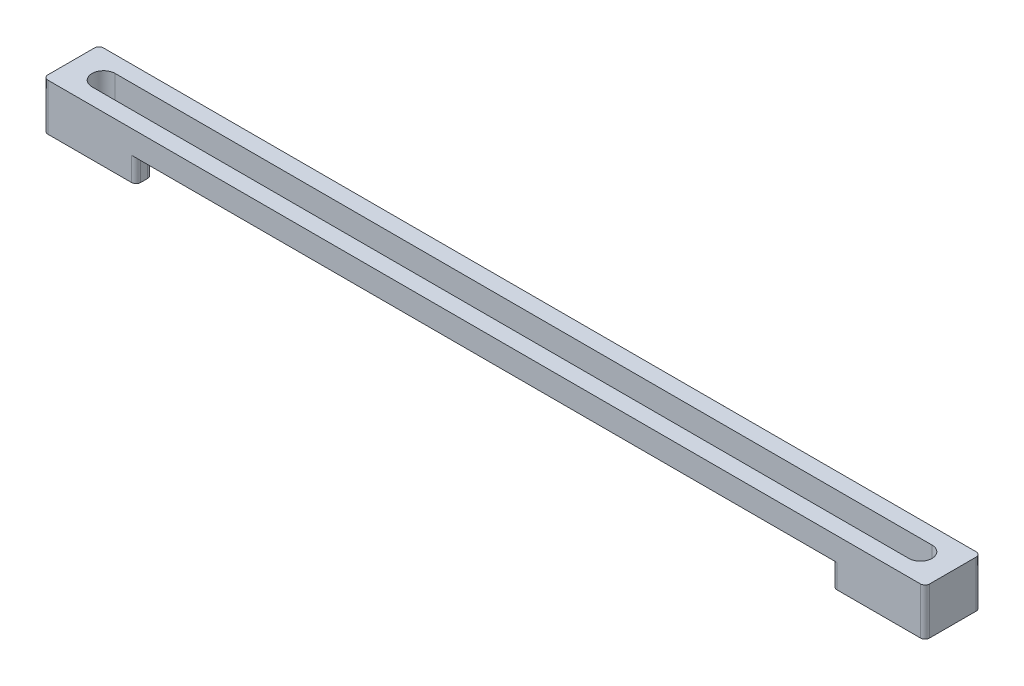
SolidWorks part; units mm, degrees
ref_plane "Plan de face" through (0, 0, 0) normal (0, 0, 1) x (1, 0, 0)
ref_plane "Plan de dessus" through (0, 0, 0) normal (0, 1, 0) x (1, 0, 0)
ref_plane "Plan de droite" through (0, 0, 0) normal (1, 0, 0) x (0, 0, -1)
sketch "Esquisse1" plane through (0, 0, 0) normal (0, 1, 0) x (1, 0, 0)
  line L0 (-88, 0) -> (88, 0) construction
  line L1 (-95, -6) -> (95, -6)
  line L2 (-95, -6) -> (-95, 6)
  line L3 (-95, 6) -> (95, 6)
  line L4 (95, -6) -> (95, 6)
  line L5 (-95, -6) -> (95, 6) construction
  line L6 (-95, 6) -> (95, -6) construction
  line L7 (-88, 2.5) -> (88, 2.5)
  line L8 (-88, -2.5) -> (88, -2.5)
  arc A0 (-88, 2.5) -> (-88, -2.5) centre (-88, 0) ccw
  arc A1 (88, -2.5) -> (88, 2.5) centre (88, 0) ccw
  point P0 (0, 0)
  point P8 (0, 0)
  dimension "D2" = 2.5
  dimension "D1" = 7
  dimension "D3" = 12
  dimension "D4" = 7
  dimension "D5" = 190
extrude "Boss.-Extru.1" add sketch "Esquisse1" along normal mid plane 5
sketch "Esquisse4" plane through (0, -2.5, 0) normal (0, -1, 0) x (1, 0, 0)
  line L0 (95, -6) -> (-95, -6) construction
  line L1 (-95, 6) -> (-75, 6)
  line L2 (-95, 6) -> (-95, -6)
  line L3 (-95, -6) -> (-75, -6)
  line L4 (-75, 6) -> (-75, 2.5)
  line L5 (-88, 0) -> (-95, 0) construction
  line L6 (-88, 2.5) -> (-75, 2.5)
  line L7 (-88, -2.5) -> (-75, -2.5)
  line L8 (-75, -2.5) -> (-75, -6)
  line L9 (-88, 2.5) -> (88, 2.5) construction
  line L10 (88, -2.5) -> (-88, -2.5) construction
  arc A0 (-88, 2.5) -> (-88, -2.5) centre (-88, 0) ccw
  arc A2 (-88, 2.5) -> (-88, -2.5) centre (-88, 0) ccw construction
  point P10 (-100, 0)
  dimension "D1" = 20
extrude "Boss.-Extru.3" add sketch "Esquisse4" along normal blind 5.1
mirror "Symétrie2" about plane through (0, 0, 0) normal (1, 0, 0) of "Boss.-Extru.3"
fillet "Congé1" radius 1 12 edges at (75, -5.05, 2.5) (75, -5.05, 6) (-75, -5.05, 2.5) (-75, -5.05, -6) (75, -5.05, -6) (75, -5.05, -2.5) (95, -2.55, -6) (-95, -2.55, -6) (-75, -5.05, -2.5) (95, -2.55, 6) (-75, -5.05, 6) (-95, -2.55, 6)
